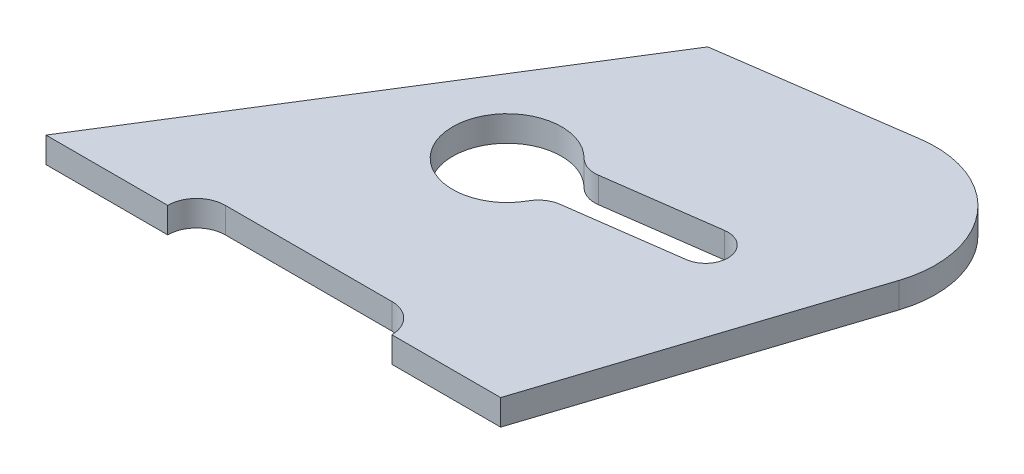
SolidWorks part; units mm, degrees
ref_plane "Front Plane" through (0, 0, 0) normal (0, 0, 1) x (1, 0, 0)
ref_plane "Top Plane" through (0, 0, 0) normal (0, 1, 0) x (1, 0, 0)
ref_plane "Right Plane" through (0, 0, 0) normal (1, 0, 0) x (0, 0, -1)
sketch "Sketch1" plane through (0, 0, 0) normal (0, 1, 0) x (1, 0, 0)
  line L0 (0, 0) -> (38, 0)
  line L1 (0, 0) -> (79.4879, 127.2072)
  line L2 (47, 9) -> (99, 9)
  line L3 (108, 0) -> (142, 0)
  line L4 (142, 0) -> (172.5035, 93.8803)
  line L5 (79.4879, 127.2072) -> (137.573, 135.4513)
  line L8 (97.1091, 75.4282) -> (131.7851, 80.1799)
  line L9 (99.0098, 61.5578) -> (133.6858, 66.3096)
  line L10 (139.6706, 74.1951) -> (167.3394, 77.9866) construction
  arc A0 (47, 9) -> (38, 0) centre (47, 0) ccw
  arc A1 (108, 0) -> (99, 9) centre (99, 0) ccw
  arc A2 (172.5035, 93.8803) -> (137.573, 135.4513) centre (142.0697, 103.7688) ccw
  arc A4 (133.6858, 66.3096) -> (131.7851, 80.1799) centre (132.7354, 73.2448) ccw
  arc A5 (90.3339, 77.7297) -> (93.1035, 57.5186) centre (78.2447, 65.7777) ccw
  arc A6 (97.1091, 75.4282) -> (90.3339, 77.7297) centre (96.023, 83.3541) cw
  arc A7 (99.0098, 61.5578) -> (93.1035, 57.5186) centre (100.0959, 53.6319) ccw
  point P13 (188.3525, 142.6585)
  point P14 (37.6243, 60.2114)
  point P15 (167.3394, 77.9866)
  point P20 (105.49, 69.5112)
  dimension "D9" = 32
  dimension "D12" = 17
  dimension "D13" = 8
  dimension "D1" = 58
  dimension "D2" = 9
  dimension "D3" = 142
  dimension "D4" = 47
  dimension "D5" = 52
  dimension "D6" = 150
  dimension "D7" = 150
  dimension "D8" = 108
  dimension "D10" = 71
  dimension "D11" = 82
  dimension "D14" = 14
extrude "Boss-Extrude1" add sketch "Sketch1" along normal blind 8
